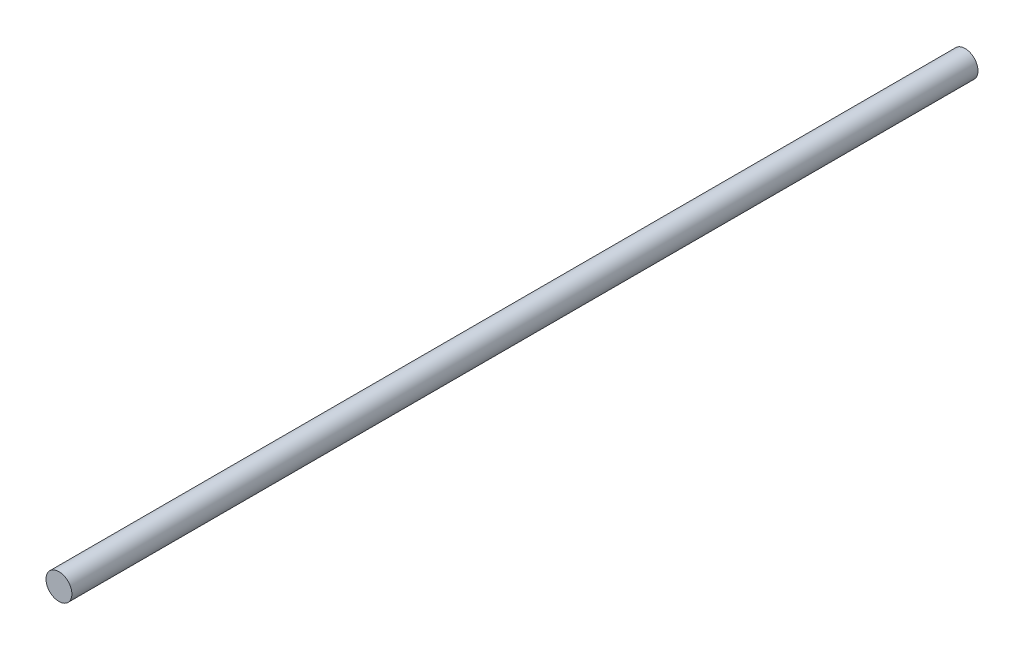
SolidWorks part; units mm, degrees
ref_plane "Alzado" through (0, 0, 0) normal (0, 0, 1) x (1, 0, 0)
ref_plane "Planta" through (0, 0, 0) normal (0, 1, 0) x (1, 0, 0)
ref_plane "Vista lateral" through (0, 0, 0) normal (1, 0, 0) x (0, 0, -1)
sketch "Croquis1" plane through (0, 0, 0) normal (0, 0, 1) x (1, 0, 0)
  circle A0 centre (0, 0) radius 4
  dimension "D1" = 8
extrude "Saliente-Extruir1" add sketch "Croquis1" along normal blind 280
